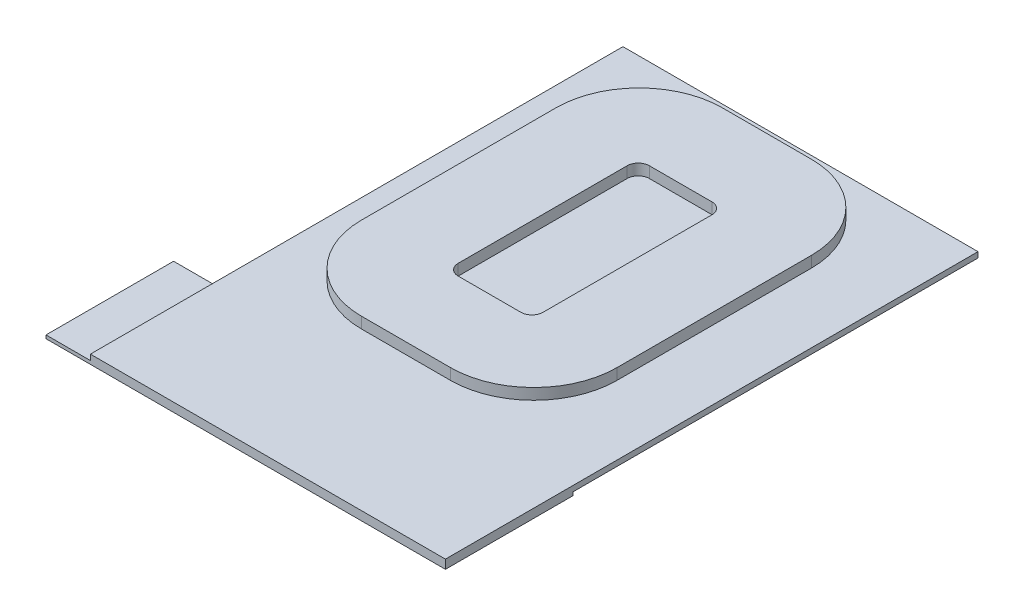
SolidWorks part; units mm, degrees
ref_plane "Front Plane" through (0, 0, 0) normal (0, 0, 1) x (1, 0, 0)
ref_plane "Top Plane" through (0, 0, 0) normal (0, 1, 0) x (1, 0, 0)
ref_plane "Right Plane" through (0, 0, 0) normal (1, 0, 0) x (0, 0, -1)
sketch "Sketch1" plane through (0, 0, 0) normal (0, 1, 0) x (1, 0, 0)
  line L1 (-16, -24) -> (16, -24)
  line L2 (-16, -24) -> (-16, 24)
  line L3 (-16, 24) -> (16, 24)
  line L4 (16, -24) -> (16, 24)
  line L5 (-16, -24) -> (16, 24) construction
  line L6 (-16, 24) -> (16, -24) construction
  point P0 (0, 0)
  dimension "D1" = 48
  dimension "D2" = 32
extrude "Boss-Extrude1" add sketch "Sketch1" along normal blind 0.5
sketch "Sketch2" plane through (0, 0.5, 0) normal (0, 1, 0) x (1, 0, 0)
  line L1 (-4.5152, 14.895) -> (1.1336, 14.895)
  line L2 (-5.5152, 13.895) -> (-5.5152, -1.3349)
  line L3 (-4.5152, -2.3349) -> (1.1336, -2.3349)
  line L4 (2.1336, 13.895) -> (2.1336, -1.3349)
  line L5 (-5.7444, 22.7047) -> (2.2824, 22.7047)
  line L6 (-13.2444, 15.2047) -> (-13.2444, -2.3226)
  line L7 (-5.7444, -9.8226) -> (2.2824, -9.8226)
  line L8 (9.7824, 15.2047) -> (9.7824, -2.3226)
  arc A0 (-13.2444, -2.3226) -> (-5.7444, -9.8226) centre (-5.7444, -2.3226) ccw
  arc A1 (2.2824, -9.8226) -> (9.7824, -2.3226) centre (2.2824, -2.3226) ccw
  arc A2 (2.2824, 22.7047) -> (9.7824, 15.2047) centre (2.2824, 15.2047) cw
  arc A3 (-5.7444, 22.7047) -> (-13.2444, 15.2047) centre (-5.7444, 15.2047) ccw
  arc A4 (-4.5152, 14.895) -> (-5.5152, 13.895) centre (-4.5152, 13.895) ccw
  arc A5 (1.1336, 14.895) -> (2.1336, 13.895) centre (1.1336, 13.895) cw
  arc A6 (1.1336, -2.3349) -> (2.1336, -1.3349) centre (1.1336, -1.3349) ccw
  arc A7 (-5.5152, -1.3349) -> (-4.5152, -2.3349) centre (-4.5152, -1.3349) ccw
  dimension "D1" = 7.5
  dimension "D2" = 1
extrude "Boss-Extrude2" add sketch "Sketch2" along normal blind 1
sketch "Sketch3" plane through (0, 0, 0) normal (0, -1, 0) x (1, 0, 0)
  line L1 (16, 24) -> (-20, 24)
  line L2 (16, 24) -> (16, 12.5)
  line L3 (16, 12.5) -> (-20, 12.5)
  line L4 (-20, 24) -> (-20, 12.5)
  dimension "D1" = 36
  dimension "D2" = 11.5
extrude "Boss-Extrude3" add sketch "Sketch3" along normal blind 0.3
